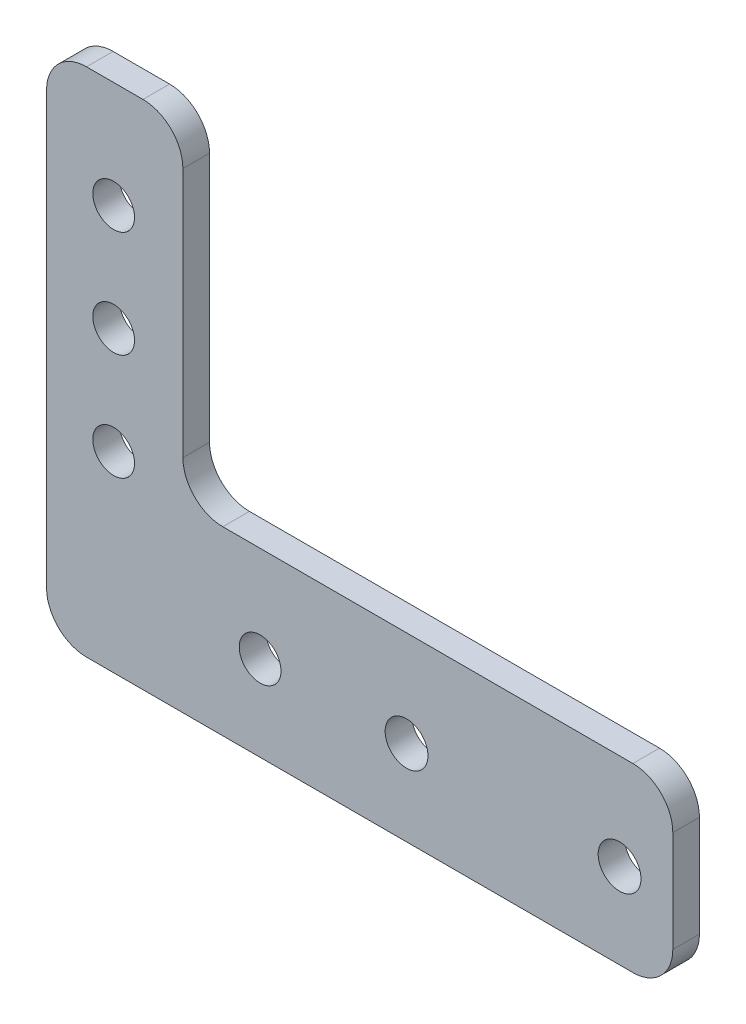
SolidWorks part; units mm, degrees
material "6061-T6 (SS)"
ref_plane "Front Plane" through (0, 0, 0) normal (0, 0, 1) x (1, 0, 0)
ref_plane "Top Plane" through (0, 0, 0) normal (0, 1, 0) x (1, 0, 0)
ref_plane "Right Plane" through (0, 0, 0) normal (1, 0, 0) x (0, 0, -1)
sketch "Sketch1" plane through (0, 0, 0) normal (0, 0, 1) x (1, 0, 0)
  line L1 (-41.275, -31.75) -> (41.275, -31.75)
  line L2 (-41.275, -31.75) -> (-41.275, 31.75)
  line L3 (-41.275, 31.75) -> (41.275, 31.75)
  line L4 (41.275, -31.75) -> (41.275, 31.75)
  line L5 (-41.275, -31.75) -> (41.275, 31.75) construction
  line L6 (-41.275, 31.75) -> (41.275, -31.75) construction
  line L7 (41.275, 31.75) -> (-17.145, 31.75)
  line L8 (41.275, 31.75) -> (41.275, -7.62)
  line L9 (41.275, -7.62) -> (-17.145, -7.62)
  line L10 (-17.145, 31.75) -> (-17.145, -7.62)
  line L11 (-41.275, -31.75) -> (-33.401, -31.75)
  line L12 (-41.275, -31.75) -> (-41.275, 31.75)
  line L13 (-41.275, 31.75) -> (-33.401, 31.75)
  line L14 (-33.401, -31.75) -> (-33.401, 31.75)
  line L15 (-33.401, -31.75) -> (41.275, -31.75)
  line L16 (-33.401, -31.75) -> (-33.401, -29.21)
  line L17 (-33.401, -29.21) -> (41.275, -29.21)
  line L18 (41.275, -31.75) -> (41.275, -29.21)
  circle A0 centre (-25.4, -19.05) radius 2.4892
  circle A1 centre (-25.4, -6.35) radius 2.4892
  circle A2 centre (-25.4, 6.35) radius 2.4892
  circle A3 centre (-25.4, 19.05) radius 2.4892
  circle A4 centre (-7.9375, -19.05) radius 2.4892
  circle A5 centre (9.525, -19.05) radius 2.5527
  circle A7 centre (34.925, -19.05) radius 2.5527
  point P0 (0, 0)
  dimension "D7" = 4.9784
  dimension "D18" = 5.1054
  dimension "D15" = 50.8
  dimension "D14" = 17.4625
  dimension "D1" = 82.55
  dimension "D2" = 63.5
  dimension "D3" = 24.13
  dimension "D4" = 24.13
  dimension "D5" = 7.874
  dimension "D6" = 63.5
  dimension "D8" = 15.875
  dimension "D9" = 12.7
  dimension "D10" = 12.7
  dimension "D11" = 12.7
  dimension "D12" = 12.7
  dimension "D13" = 25.4
  dimension "D16" = 2.54
extrude "Boss-Extrude1" add sketch "Sketch1" along normal blind 3.175
fillet "Fillet1" radius 4.7625 6 edges at (-33.401, 31.75, 1.5875) (-17.145, 31.75, 1.5875) (-17.145, -7.62, 1.5875) (41.275, -7.62, 1.5875) (41.275, -29.21, 1.5875) (-33.401, -29.21, 1.5875)
